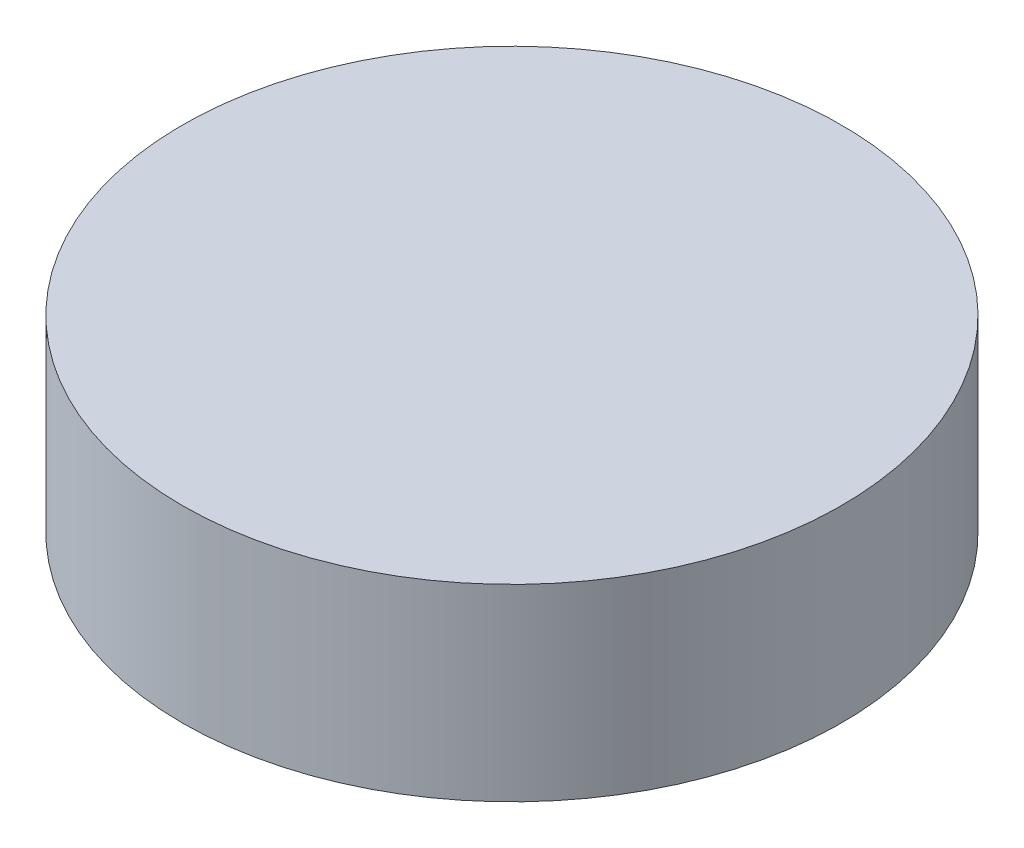
SolidWorks part; units mm, degrees
ref_plane "Front Plane" through (0, 0, 0) normal (0, 0, 1) x (1, 0, 0)
ref_plane "Top Plane" through (0, 0, 0) normal (0, 1, 0) x (1, 0, 0)
ref_plane "Right Plane" through (0, 0, 0) normal (1, 0, 0) x (0, 0, -1)
sketch "Sketch1" plane through (0, 0, 0) normal (0, 1, 0) x (1, 0, 0)
  circle A0 centre (0, 0) radius 8.75
  dimension "D1" = 17.5
extrude "Extrude1" add sketch "Sketch1" along normal blind 5
